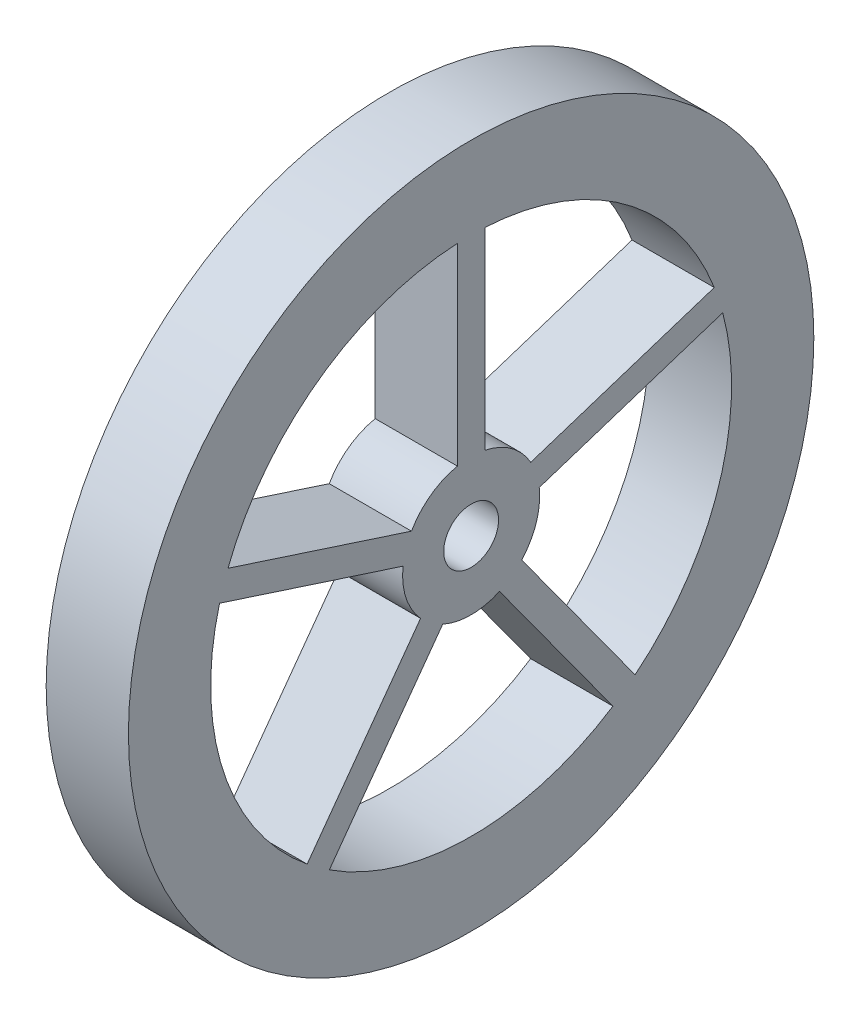
SolidWorks part; units mm, degrees
ref_plane "Front Plane" through (0, 0, 0) normal (0, 0, 1) x (1, 0, 0)
ref_plane "Top Plane" through (0, 0, 0) normal (0, 1, 0) x (1, 0, 0)
ref_plane "Right Plane" through (0, 0, 0) normal (1, 0, 0) x (0, 0, -1)
sketch "Sketch1" plane through (0, 0, 0) normal (1, 0, 0) x (0, 0, -1)
  line L0 (177.3601, 68.1424) -> (43.5019, 24.6492)
  line L2 (-10, 189.7367) -> (-10, 48.9898)
  line L4 (10, 189.7367) -> (10, 48.9898)
  line L5 (183.5405, 49.1213) -> (49.6822, 5.6281)
  line L6 (119.6146, -147.6223) -> (36.8856, -33.7557)
  line L7 (103.4342, -159.378) -> (20.7053, -45.5114)
  line L8 (-103.4342, -159.378) -> (-20.7053, -45.5114)
  line L9 (-119.6146, -147.6223) -> (-36.8856, -33.7557)
  line L10 (-183.5405, 49.1213) -> (-49.6822, 5.6281)
  line L11 (-177.3601, 68.1424) -> (-43.5019, 24.6492)
  arc A0 (-10, 48.9898) -> (-43.5019, 24.6492) centre (0, 0) ccw
  circle A1 centre (0, 0) radius 20
  arc A2 (-10, 189.7367) -> (-177.3601, 68.1424) centre (0, 0) ccw
  circle A3 centre (0, 0) radius 250
  arc A4 (43.5019, 24.6492) -> (10, 48.9898) centre (0, 0) ccw
  arc A5 (177.3601, 68.1424) -> (10, 189.7367) centre (0, 0) ccw
  arc A6 (119.6146, -147.6223) -> (183.5405, 49.1213) centre (0, 0) ccw
  arc A7 (-103.4342, -159.378) -> (103.4342, -159.378) centre (0, 0) ccw
  arc A8 (-183.5405, 49.1213) -> (-119.6146, -147.6223) centre (0, 0) ccw
  arc A9 (-49.6822, 5.6281) -> (-36.8856, -33.7557) centre (0, 0) ccw
  arc A10 (-20.7053, -45.5114) -> (20.7053, -45.5114) centre (0, 0) ccw
  arc A11 (36.8856, -33.7557) -> (49.6822, 5.6281) centre (0, 0) ccw
  point P29 (0, 0)
  dimension "D1" = 500
  dimension "D2" = 380
  dimension "D3" = 5
sketch "Sketch2" plane through (0, 0, 0) normal (1, 0, 0) x (0, 0, -1)
extrude "Boss-Extrude1" add sketch "Sketch1" along normal blind 60
